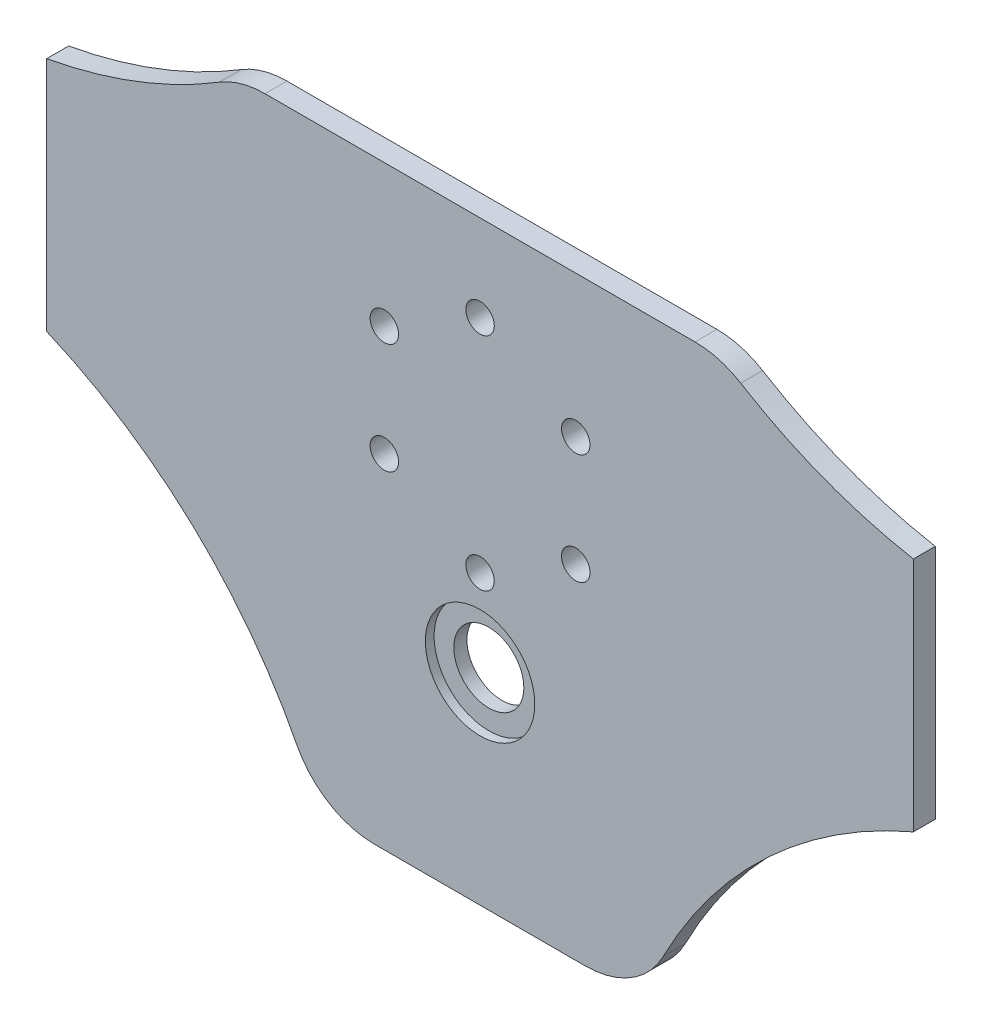
SolidWorks part; units mm, degrees
ref_plane "Plano frontal" through (0, 0, 0) normal (0, 0, 1) x (1, 0, 0)
ref_plane "Plano superior" through (0, 0, 0) normal (0, 1, 0) x (1, 0, 0)
ref_plane "Plano direito" through (0, 0, 0) normal (1, 0, 0) x (0, 0, -1)
sketch "Esboço1" plane through (0, 0, 0) normal (0, 0, 1) x (1, 0, 0)
  line L0 (-49.1191, 68) -> (49.1191, 68)
  line L1 (0, -5.5) -> (0, -8.5) construction
  line L3 (-24.2376, -63) -> (24.2376, -63) construction
  line L4 (99, -68) -> (99, 68) construction
  line L5 (-44, 55.5) -> (44, 55.5) construction
  line L6 (-44, -9.5) -> (-44, 55.5) construction
  line L7 (-88.0945, 47.3219) -> (-88.0945, 52.54) construction
  line L8 (-24.1062, -68) -> (24.1062, -68)
  line L9 (99, 23) -> (-99, 23) construction
  line L10 (99, -4) -> (99, 50)
  line L11 (0, 54.5) -> (0, 51.5) construction
  line L12 (0, -8.5) -> (0, -9.5) construction
  line L14 (-46.5, -12) -> (-46.5, 58) construction
  line L19 (-88.1314, -3.7131) -> (-88.1314, -9.3321) construction
  line L20 (-88.1314, -9.3321) -> (-88.1314, -3.7131) construction
  line L22 (88.1314, -9.3321) -> (88.1314, -3.7131) construction
  line L24 (88.1314, -3.7131) -> (88.1314, -9.3321) construction
  line L25 (-40, 48.5) -> (40, 48.5) construction
  line L29 (0, 68) -> (0, -68) construction
  line L32 (-40, -2.5) -> (-40, 48.5) construction
  line L35 (-46.5, -12) -> (46.5, -12) construction
  line L36 (-99, -4) -> (-99, 50)
  line L37 (-46.5, 58) -> (46.5, 58) construction
  line L38 (46.5, -12) -> (46.5, 58) construction
  line L39 (-41.2651, 62.9464) -> (41.2651, 62.9464) construction
  line L42 (-40, -2.5) -> (40, -2.5) construction
  line L45 (40, -2.5) -> (40, 48.5) construction
  line L48 (88.0945, 47.3219) -> (88.0945, 52.54) construction
  line L49 (-44, -9.5) -> (44, -9.5) construction
  line L53 (44, -9.5) -> (44, 55.5) construction
  line L54 (-24.1062, -68) -> (24.1062, -68) construction
  arc A0 (-49.5046, 58.613) -> (-55.6588, 56.879) centre (-53.6243, 61.4464) cw construction
  arc A1 (99, 50) -> (59.5611, 65.0577) centre (119.6025, 163.1395) cw
  arc A2 (-51.1834, -34.0488) -> (-52.2174, -26.9468) centre (-45.7528, -29.6318) cw construction
  arc A3 (41.8901, -57.1507) -> (99, -4) centre (144.147, -109.7674) cw
  circle A4 centre (0, 23) radius 31.5 construction
  arc A5 (-50.4763, -34.9265) -> (-51.1834, -34.0488) centre (-144.2784, -109.7674) ccw construction
  arc A6 (-37.5755, -54.863) -> (-50.4763, -34.9265) centre (-144.2784, -109.7674) ccw construction
  circle A7 centre (0, 48.25) radius 3.25
  arc A8 (-24.2376, -63) -> (-37.5755, -54.863) centre (-24.2376, -48) cw construction
  arc A9 (-49.5046, 58.613) -> (-41.2651, 62.9464) centre (-41.2651, 52.9464) cw construction
  circle A10 centre (21.8671, 35.625) radius 3.25
  circle A11 centre (21.8671, 10.375) radius 3.25
  arc A12 (-65.6729, -19.0968) -> (-58.6068, -20.3533) centre (-61.0875, -13.8076) ccw construction
  arc A13 (-64.3407, 56.6167) -> (-55.6588, 56.879) centre (-59.7277, 47.7442) cw construction
  arc A14 (24.1062, -68) -> (41.8901, -57.1507) centre (24.1062, -48) ccw
  arc A15 (59.5611, 65.0577) -> (49.1191, 68) centre (49.1191, 48) ccw
  arc A16 (-65.6729, -19.0968) -> (-88.1314, -3.7131) centre (-144.2784, -109.7674) ccw construction
  arc A17 (-88.0945, 47.3219) -> (-64.3407, 56.6167) centre (-119.697, 163.0858) ccw construction
  arc A18 (-58.6068, -20.3533) -> (-52.2174, -26.9468) centre (-56.8349, -25.0288) cw construction
  circle A19 centre (-53.6243, 61.4464) radius 3 construction
  circle A20 centre (-56.8349, -25.0288) radius 3 construction
  circle A21 centre (-44, 55.5) radius 1.5 construction
  circle A22 centre (-44, -9.5) radius 1.5 construction
  arc A23 (-59.5611, 65.0577) -> (-49.1191, 68) centre (-49.1191, 48) cw
  arc A24 (58.6068, -20.3533) -> (52.2174, -26.9468) centre (56.8349, -25.0288) ccw construction
  arc A25 (88.0945, 47.3219) -> (64.3407, 56.6167) centre (119.697, 163.0858) cw construction
  arc A26 (65.6729, -19.0968) -> (88.1314, -3.7131) centre (144.2784, -109.7674) cw construction
  arc A27 (64.3407, 56.6167) -> (55.6588, 56.879) centre (59.7277, 47.7442) ccw construction
  arc A28 (65.6729, -19.0968) -> (58.6068, -20.3533) centre (61.0875, -13.8076) cw construction
  arc A29 (49.5046, 58.613) -> (41.2651, 62.9464) centre (41.2651, 52.9464) ccw construction
  circle A30 centre (44, -9.5) radius 1.5 construction
  arc A31 (-24.1062, -68) -> (-41.8901, -57.1507) centre (-24.1062, -48) cw
  circle A32 centre (44, 55.5) radius 1.5 construction
  circle A33 centre (56.8349, -25.0288) radius 3 construction
  arc A34 (24.2376, -63) -> (37.5755, -54.863) centre (24.2376, -48) ccw construction
  arc A35 (37.5755, -54.863) -> (50.4763, -34.9265) centre (144.2784, -109.7674) cw construction
  circle A36 centre (0, -2.25) radius 3.25
  circle A37 centre (-21.8671, 10.375) radius 3.25
  circle A38 centre (-21.8671, 35.625) radius 3.25
  circle A39 centre (53.6243, 61.4464) radius 3 construction
  arc A40 (50.4763, -34.9265) -> (51.1834, -34.0488) centre (144.2784, -109.7674) cw construction
  arc A41 (51.1834, -34.0488) -> (52.2174, -26.9468) centre (45.7528, -29.6318) ccw construction
  circle A42 centre (0, -22) radius 12.5 construction
  arc A43 (-41.8901, -57.1507) -> (-99, -4) centre (-144.147, -109.7674) ccw
  arc A44 (-99, 50) -> (-59.5611, 65.0577) centre (-119.6025, 163.1395) ccw
  circle A45 centre (0, -22) radius 8
  arc A46 (49.5046, 58.613) -> (55.6588, 56.879) centre (53.6243, 61.4464) ccw construction
  point P59 (0, 23)
  point P84 (0, 23)
  point P86 (0, 23)
  point P99 (0, 23)
  point P107 (0, 22.9993)
  dimension "D3" = 57
  dimension "D1" = 6
  dimension "D2" = 136
  dimension "D5" = 64
extrude "Ressalto-extrusão1" add sketch "Esboço1" along normal blind 5
sketch "Esboço2" plane through (0, 0, 5) normal (0, 0, 1) x (1, 0, 0)
  circle A0 centre (0, -22) radius 12.5
  circle A1 centre (0, -22) radius 8
extrude "Corte-extrusão1" cut sketch "Esboço2" against normal blind 2
